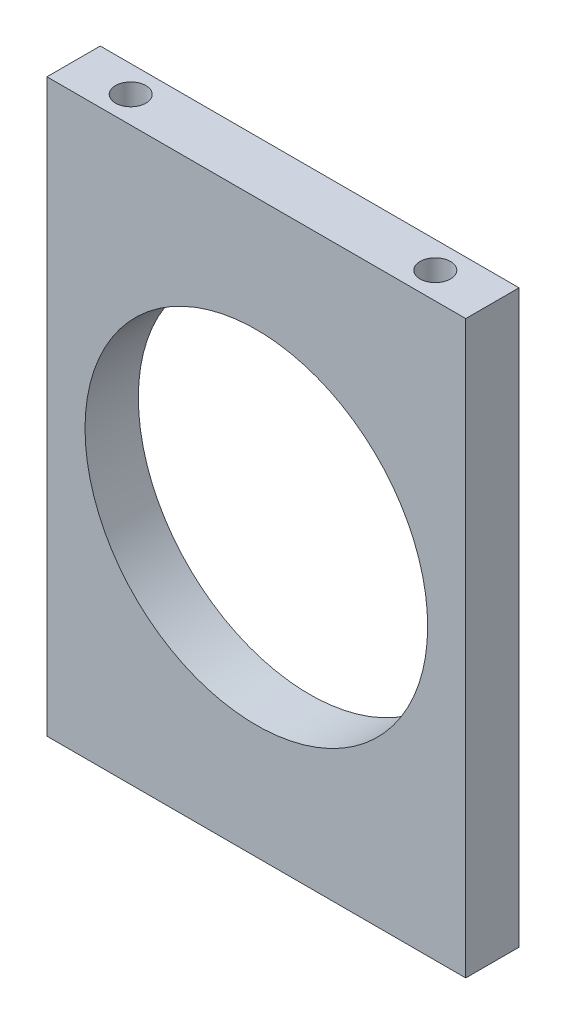
SolidWorks part; units mm, degrees
ref_plane "Front Plane" through (0, 0, 0) normal (0, 0, 1) x (1, 0, 0)
ref_plane "Top Plane" through (0, 0, 0) normal (0, 1, 0) x (1, 0, 0)
ref_plane "Right Plane" through (0, 0, 0) normal (1, 0, 0) x (0, 0, -1)
sketch "Sketch1" plane through (0, 0, 0) normal (0, 0, 1) x (1, 0, 0)
  line L1 (-27.5, 37.5) -> (27.5, 37.5)
  line L2 (-27.5, 37.5) -> (-27.5, -37.5)
  line L3 (-27.5, -37.5) -> (27.5, -37.5)
  line L4 (27.5, 37.5) -> (27.5, -37.5)
  line L5 (-27.5, 37.5) -> (27.5, -37.5) construction
  line L6 (-27.5, -37.5) -> (27.5, 37.5) construction
  circle A0 centre (0, 0) radius 22.5
  point P0 (0, 0)
  dimension "D3" = 45
  dimension "D1" = 55
  dimension "D2" = 75
extrude "Boss-Extrude1" add sketch "Sketch1" along normal blind 7
sketch "Sketch2" plane through (0, 37.5, 0) normal (0, 1, 0) x (1, 0, 0)
  line L0 (0, 0) -> (0, -7) construction
  line L1 (27.5, -7) -> (-27.5, -7) construction
  line L2 (27.5, 0) -> (-27.5, 0) construction
  circle A0 centre (-20, -3.5) radius 2
  circle A1 centre (20, -3.5) radius 2
  dimension "D1" = 4
  dimension "D2" = 3.5
  dimension "D3" = 20
extrude "Cut-Extrude1" cut sketch "Sketch2" against normal blind 15
sketch "Sketch3" plane through (0, -37.5, 0) normal (0, -1, 0) x (1, 0, 0)
  line L0 (0, 0) -> (0, 7) construction
  line L1 (-27.5, 7) -> (27.5, 7) construction
  circle A0 centre (-20, 3.5) radius 2
  circle A1 centre (20, 3.5) radius 2
  dimension "D1" = 4
  dimension "D2" = 3.5
  dimension "D3" = 20
extrude "Cut-Extrude2" cut sketch "Sketch3" against normal blind 15
